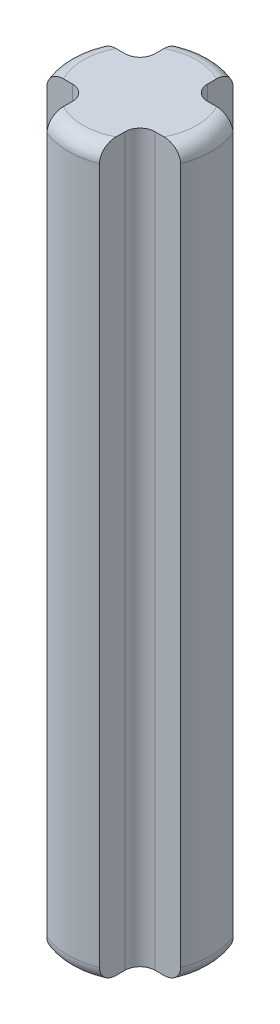
SolidWorks part; units mm, degrees
ref_plane "Front Plane" through (0, 0, 0) normal (0, 0, 1) x (1, 0, 0)
ref_plane "Top Plane" through (0, 0, 0) normal (0, 1, 0) x (1, 0, 0)
ref_plane "Right Plane" through (0, 0, 0) normal (1, 0, 0) x (0, 0, -1)
ref_plane "Plane1" through (0, 0, 0) normal (0, 0, -1) x (-1, 0, 0)
sketch "Sketch1" plane through (0, 0, 0) normal (0, 0, -1) x (-1, 0, 0)
  line L0 (-2.39, 0) -> (0, 0)
  line L1 (0, 0) -> (0, 24.195)
  line L2 (0, 24.195) -> (-2.39, 24.195)
  line L3 (-2.39, 24.195) -> (-2.39, 0)
  line L4 (0, 0) -> (0, 24.195) construction
revolve "Revolve1" add sketch "Sketch1" angle 360 about L4
sketch "Sketch2" plane through (0, 0, 0) normal (0, -1, 0) x (1, 0, 0)
  line L0 (0.875, 2.2241) -> (0.875, 0.875)
  line L1 (0.875, 0.875) -> (2.2241, 0.875)
  arc A0 (2.2241, 0.875) -> (0.875, 2.2241) centre (0, 0) ccw
extrude "Cut-Extrude1" cut sketch "Sketch2" against normal through all
sketch "Sketch3" plane through (0, 0, 0) normal (0, -1, 0) x (1, 0, 0)
  line L0 (2.2241, -0.875) -> (0.875, -0.875)
  line L1 (0.875, -0.875) -> (0.875, -2.2241)
  arc A0 (0.875, -2.2241) -> (2.2241, -0.875) centre (0, 0) ccw
extrude "Cut-Extrude2" cut sketch "Sketch3" against normal through all
sketch "Sketch4" plane through (0, 0, 0) normal (0, -1, 0) x (1, 0, 0)
  line L0 (-0.875, -2.2241) -> (-0.875, -0.875)
  line L1 (-0.875, -0.875) -> (-2.2241, -0.875)
  arc A0 (-2.2241, -0.875) -> (-0.875, -2.2241) centre (0, 0) ccw
extrude "Cut-Extrude3" cut sketch "Sketch4" against normal through all
sketch "Sketch5" plane through (0, 0, 0) normal (0, -1, 0) x (1, 0, 0)
  line L0 (-2.2241, 0.875) -> (-0.875, 0.875)
  line L1 (-0.875, 0.875) -> (-0.875, 2.2241)
  arc A0 (-0.875, 2.2241) -> (-2.2241, 0.875) centre (0, 0) ccw
extrude "Cut-Extrude4" cut sketch "Sketch5" against normal through all
fillet "Fillet1" radius 0.5 12 edges at (-2.39, 24.195, 0) (-2.39, 0, 0) (2.39, 0, 0) (0.875, 12.0975, -0.875) (0, 24.195, -2.39) (-0.875, 12.0975, 0.875) (0, 0, 2.39) (-0.875, 12.0975, -0.875) (0, 0, -2.39) (0, 24.195, 2.39) (0.875, 12.0975, 0.875) (2.39, 24.195, 0)
